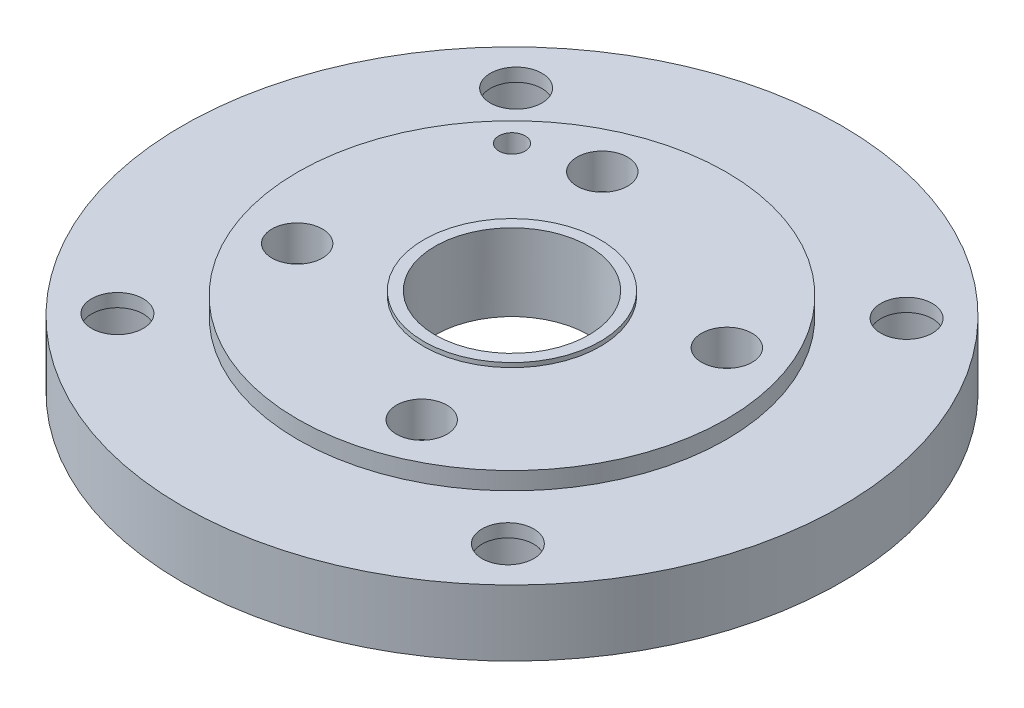
SolidWorks part; units mm, degrees
ref_plane "Ön Düzlem" through (0, 0, 0) normal (0, 0, 1) x (1, 0, 0)
ref_plane "Üst Düzlem" through (0, 0, 0) normal (0, 1, 0) x (1, 0, 0)
ref_plane "Sağ Düzlem" through (0, 0, 0) normal (1, 0, 0) x (0, 0, -1)
sketch "Çizim1" plane through (0, 0, 0) normal (0, 1, 0) x (1, 0, 0)
  circle A0 centre (0, 0) radius 150
  dimension "D1" = 300
extrude "Yükseklik-Ekstrüzyon1" add sketch "Çizim1" along normal blind 30
sketch "Çizim2" plane through (0, 30, 0) normal (0, 1, 0) x (1, 0, 0)
  circle A0 centre (0, 0) radius 97.5
  dimension "D1" = 195
extrude "Yükseklik-Ekstrüzyon2" add sketch "Çizim2" along normal blind 8
sketch "Çizim3" plane through (0, 38, 0) normal (0, 1, 0) x (1, 0, 0)
  circle A0 centre (0, 0) radius 40.15
  dimension "D1" = 80.3
extrude "Yükseklik-Ekstrüzyon3" add sketch "Çizim3" along normal blind 2
sketch "Çizim4" plane through (0, 40, 0) normal (0, 1, 0) x (1, 0, 0)
  circle A0 centre (0, 0) radius 35
  dimension "D1" = 70
extrude "Kes-Ekstrüzyon1" cut sketch "Çizim4" against normal through all
sketch "Çizim5" plane through (0, 0, 0) normal (0, -1, 0) x (1, 0, 0)
  circle A0 centre (0, 0) radius 43.5
  dimension "D1" = 87
extrude "Kes-Ekstrüzyon2" cut sketch "Çizim5" against normal blind 5
sketch "Çizim6" plane through (0, 38, 0) normal (0, 1, 0) x (1, 0, 0)
  line L0 (0, -161.9499) -> (0, 161.9499) construction
  line L1 (-245.4148, 0) -> (245.4148, 0) construction
  line L2 (0, 0) -> (-52.5778, 128.8379) construction
  line L3 (0, 0) -> (66.0728, -161.9065) construction
  line L4 (0, 0) -> (-120.287, 122.833) construction
  circle A0 centre (0, 0) radius 75 construction
  circle A1 centre (0, 0) radius 127 construction
  circle A2 centre (-28.3381, 69.4403) radius 11.5
  circle A3 centre (69.4403, 28.3381) radius 11.5
  circle A4 centre (28.3381, -69.4403) radius 11.5
  circle A5 centre (-69.4403, -28.3381) radius 11.5
  circle A6 centre (-60, 60) radius 6
  point P5 (0, 0)
  point P9 (0, 0)
  point P25 (0, 0)
  point P26 (0, 0)
  dimension "D1" = 150
  dimension "D2" = 254
  dimension "D5" = 23
  dimension "D7" = 22.2
  dimension "D8" = 12
  dimension "D3" = 22.2
  dimension "D4" = 22.2
  dimension "D9" = 60
  dimension "D10" = 60
  dimension "D6" = 4
extrude "Kes-Ekstrüzyon4" cut sketch "Çizim6" against normal blind 16
sketch "Çizim7" plane through (0, 30, 0) normal (0, 1, 0) x (1, 0, 0)
  line L0 (0, -206.8178) -> (0, 206.8178) construction
  line L1 (-215.1364, 0) -> (215.1364, 0) construction
  line L2 (88.8572, -90.738) -> (-88.8572, 90.738) construction
  circle A0 centre (0, 0) radius 127 construction
  circle A1 centre (-88.8572, 90.738) radius 11.75
  circle A2 centre (90.738, 88.8572) radius 11.75
  circle A3 centre (88.8572, -90.738) radius 11.75
  circle A4 centre (-90.738, -88.8572) radius 11.75
  point P5 (0, 0)
  point P10 (0, 0)
  point P14 (0, 0)
  point P17 (0, 0)
  point P25 (0, 0)
  dimension "D1" = 254
  dimension "D2" = 23.5
  dimension "D3" = 44.4
  dimension "D4" = 4
extrude "Kes-Ekstrüzyon5" cut sketch "Çizim7" against normal through all
sketch "Çizim8" plane through (0, 22, 0) normal (0, 1, 0) x (1, 0, 0)
  circle A0 centre (-60, 60) radius 6 construction
  circle A1 centre (-60, 60) radius 6
extrude "Kes-Ekstrüzyon6" cut sketch "Çizim8" against normal through all
sketch "Çizim9" plane through (0, 0, 0) normal (0, -1, 0) x (1, 0, 0)
  circle A0 centre (-90.738, 88.8572) radius 17.5
  circle A1 centre (88.8572, 90.738) radius 17.5
  circle A2 centre (90.738, -88.8572) radius 17.5
  circle A3 centre (-88.8572, -90.738) radius 17.5
  point P3 (-88.8572, -90.738)
  point P12 (0, 0)
  dimension "D1" = 35
  dimension "D2" = 4
extrude "Kes-Ekstrüzyon7" cut sketch "Çizim9" against normal blind 24
